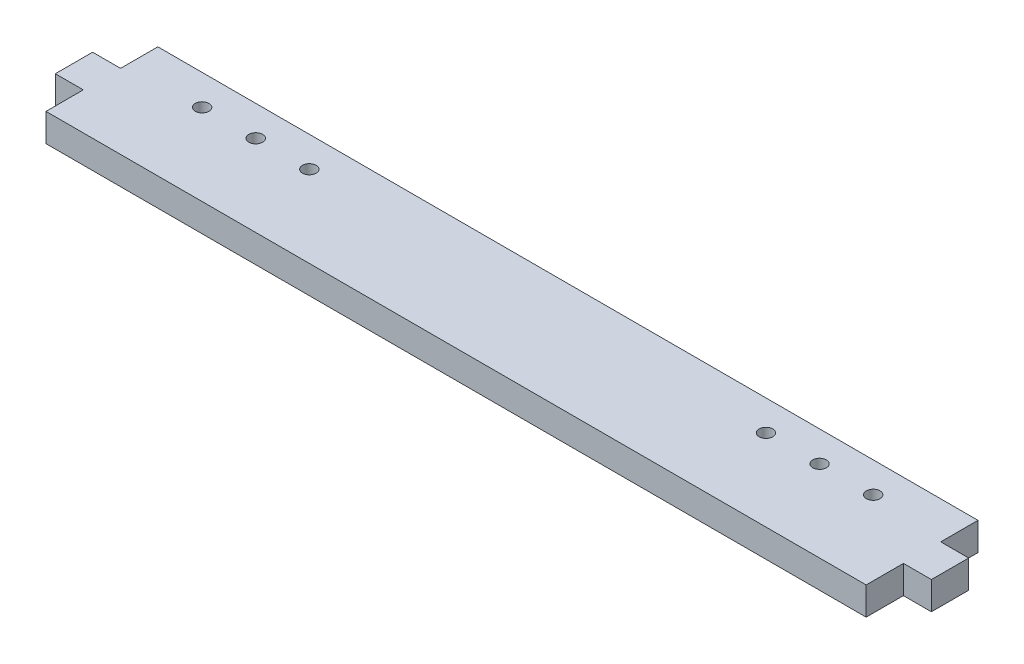
SolidWorks part; units mm, degrees
ref_plane "Front Plane" through (0, 0, 0) normal (0, 0, 1) x (1, 0, 0)
ref_plane "Top Plane" through (0, 0, 0) normal (0, 1, 0) x (1, 0, 0)
ref_plane "Right Plane" through (0, 0, 0) normal (1, 0, 0) x (0, 0, -1)
sketch "Sketch1" plane through (0, 0, 0) normal (0, 1, 0) x (1, 0, 0)
  line L1 (139.7, -19.05) -> (-139.7, -19.05)
  line L2 (139.7, -19.05) -> (139.7, 19.05)
  line L3 (139.7, 19.05) -> (-139.7, 19.05)
  line L4 (-139.7, -19.05) -> (-139.7, 19.05)
  line L5 (139.7, -19.05) -> (-139.7, 19.05) construction
  line L6 (139.7, 19.05) -> (-139.7, -19.05) construction
  point P0 (0, 0)
  dimension "D1" = 279.4
  dimension "D2" = 38.1
extrude "Boss-Extrude1" add sketch "Sketch1" along normal blind 9.525
sketch "Sketch2" plane through (139.7, 0, 0) normal (1, 0, 0) x (0, 0, -1)
  line L0 (-19.05, 0) -> (19.05, 0) construction
  line L1 (-6.35, 0) -> (6.35, 0)
  line L2 (-6.35, 0) -> (-6.35, 9.525)
  line L3 (-6.35, 9.525) -> (6.35, 9.525)
  line L4 (6.35, 0) -> (6.35, 9.525)
  line L5 (-19.05, 9.525) -> (19.05, 9.525) construction
  line L6 (-19.05, 9.525) -> (-19.05, 0) construction
  dimension "D1" = 12.7
  dimension "D2" = 12.7
extrude "Boss-Extrude2" add sketch "Sketch2" along normal blind 9.525
mirror "Mirror1" about plane through (0, 0, 0) normal (1, 0, 0) of "Boss-Extrude2"
sketch "Sketch3" plane through (0, 0, 0) normal (0, -1, 0) x (1, 0, 0)
  line L0 (139.7, -6.35) -> (139.7, -19.05) construction
  line L1 (139.7, -19.05) -> (-139.7, -19.05) construction
  line L2 (114.3, -19.05) -> (77.7748, -19.05) construction
  line L3 (114.3, -19.05) -> (114.3, -8.7376) construction
  line L4 (114.3, -8.7376) -> (77.7748, -8.7376) construction
  line L5 (77.7748, -19.05) -> (77.7748, -8.7376) construction
  line L6 (114.3, -19.05) -> (77.7748, -8.7376) construction
  line L7 (114.3, -8.7376) -> (77.7748, -19.05) construction
  circle A0 centre (114.3, -8.7376) radius 2.3368
  circle A1 centre (77.7748, -8.7376) radius 2.3368
  circle A2 centre (96.0374, -8.7376) radius 2.3368
  point P6 (96.0374, -13.8938)
  dimension "D4" = 4.6736
  dimension "D5" = 4.6736
  dimension "D6" = 4.6736
  dimension "D1" = 36.5252
  dimension "D2" = 10.3124
  dimension "D3" = 25.4
extrude "Cut-Extrude1" cut sketch "Sketch3" against normal through all
mirror "Mirror2" about plane through (0, 0, 0) normal (1, 0, 0) of "Cut-Extrude1"
